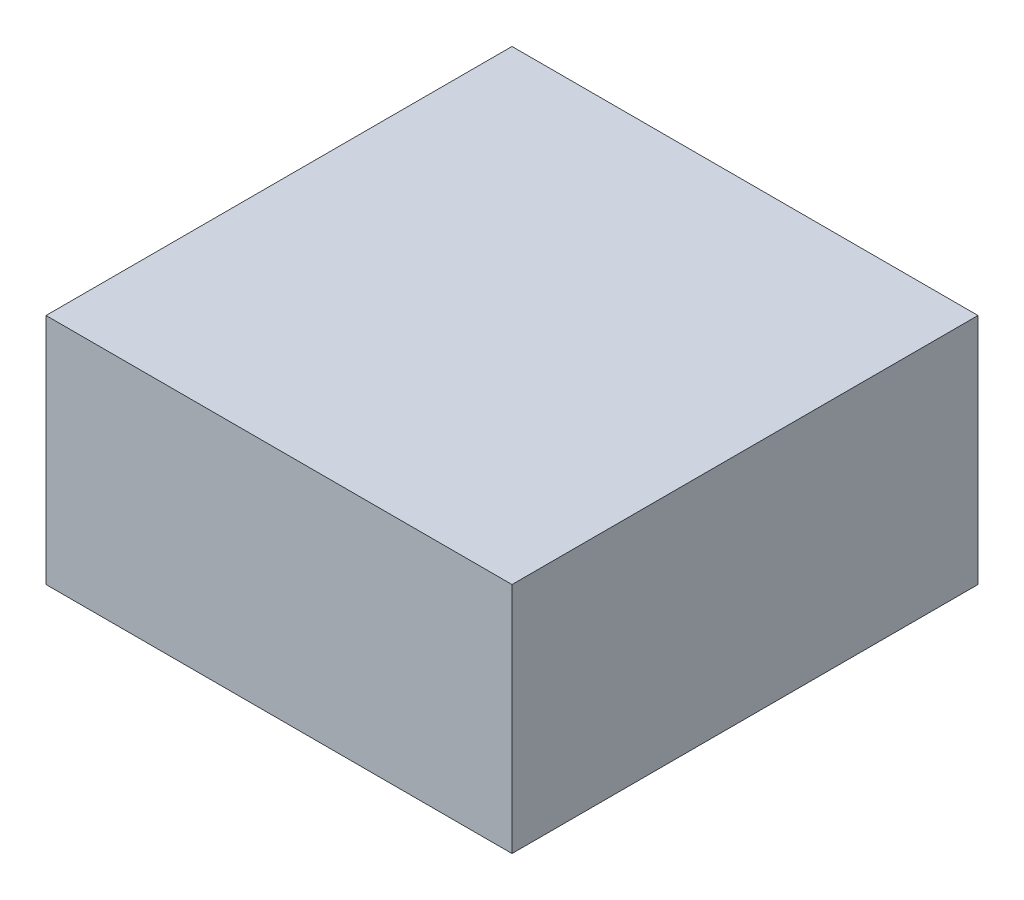
SolidWorks part; units mm, degrees
ref_plane "Front Plane" through (0, 0, 0) normal (0, 0, 1) x (1, 0, 0)
ref_plane "Top Plane" through (0, 0, 0) normal (0, 1, 0) x (1, 0, 0)
ref_plane "Right Plane" through (0, 0, 0) normal (1, 0, 0) x (0, 0, -1)
sketch "Sketch1" plane through (0, 0, 0) normal (0, 0, 1) x (1, 0, 0)
  line L1 (-100, -50) -> (100, -50)
  line L2 (-100, -50) -> (-100, 50)
  line L3 (-100, 50) -> (100, 50)
  line L4 (100, -50) -> (100, 50)
  line L5 (-100, -50) -> (100, 50) construction
  line L6 (-100, 50) -> (100, -50) construction
  point P0 (0, 0)
  dimension "D1" = 100
  dimension "D2" = 200
extrude "Boss-Extrude1" add sketch "Sketch1" along normal blind 200
